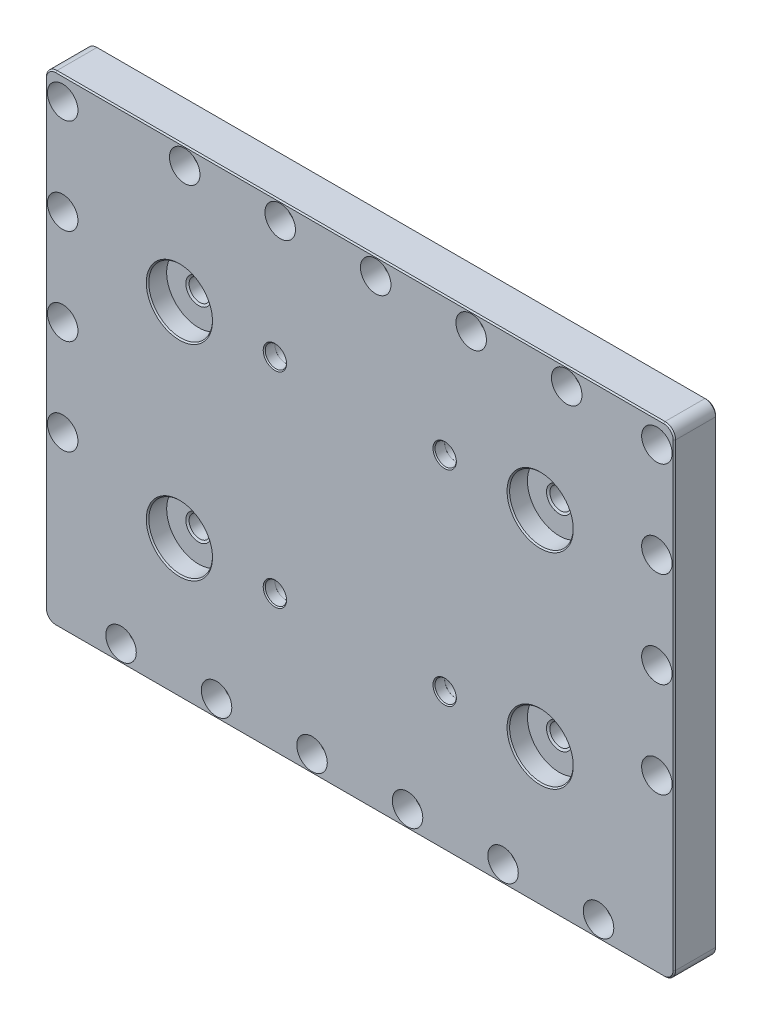
SolidWorks part; units mm, degrees
material "6061-T6 Al"
ref_plane "Front" through (0, 0, 0) normal (0, 0, 1) x (1, 0, 0)
ref_plane "Top" through (0, 0, 0) normal (0, 1, 0) x (1, 0, 0)
ref_plane "Right" through (0, 0, 0) normal (1, 0, 0) x (0, 0, -1)
sketch "Sketch1" plane through (0, 0, 0) normal (0, 0, 1) x (1, 0, 0)
  line L1 (-188.2775, 0) -> (188.2775, 0)
  line L2 (-188.2775, 0) -> (-188.2775, 287.655)
  line L3 (-188.2775, 287.655) -> (188.2775, 287.655)
  line L4 (188.2775, 0) -> (188.2775, 287.655)
  dimension "D1" = 376.555
  dimension "D2" = 287.655
extrude "Extrude1" add sketch "Sketch1" along normal blind 25.4
hole_wizard "CBORE for 3/8 Socket Head Cap Screw3" positions "Sketch8" profile "Sketch7" counterbore size "3/8" standard "Ansi Inch" end condition through all
sketch "Sketch8" plane through (0, 0, 25.4) normal (0, 0, 1) x (1, 0, 0)
  line L0 (-142.875, 10.4775) -> (-85.725, 10.4775) construction
  line L1 (-85.725, 10.4775) -> (-28.575, 10.4775) construction
  line L2 (-28.575, 10.4775) -> (28.575, 10.4775) construction
  line L3 (28.575, 10.4775) -> (85.725, 10.4775) construction
  line L7 (85.725, 10.4775) -> (142.875, 10.4775) construction
  line L14 (0, 10.4775) -> (0, 277.1775) construction
  line L17 (0, 143.8275) -> (188.2775, 143.8275) construction
  line L18 (188.2775, 0) -> (188.2775, 287.655) construction
  line L19 (-188.2775, 287.655) -> (-188.2775, 0) construction
  line L20 (-104.775, 277.1775) -> (-47.625, 277.1775) construction
  line L23 (-47.625, 277.1775) -> (9.525, 277.1775) construction
  line L24 (9.525, 277.1775) -> (66.675, 277.1775) construction
  line L25 (66.675, 277.1775) -> (123.825, 277.1775) construction
  point P0 (-142.875, 10.4775)
  point P1 (-85.725, 10.4775)
  point P3 (-28.575, 10.4775)
  point P5 (28.575, 10.4775)
  point P7 (85.725, 10.4775)
  point P37 (-104.775, 277.1775)
  point P39 (-47.625, 277.1775)
  point P41 (9.525, 277.1775)
  point P43 (66.675, 277.1775)
  point P45 (123.825, 277.1775)
  point P49 (142.875, 10.4775)
  point P78 (0, 10.4775)
  dimension "D1" = 266.7
  dimension "D2" = 57.15
  dimension "D3" = 83.5025
sketch "Sketch7" plane through (-142.875, 10.4775, 25.4) normal (1, 0, 0) x (0, -1, 0)
  line L0 (0, 0) -> (0, 25.4)
  line L1 (5.5626, 24.6126) -> (6.35, 25.4)
  line L2 (5.5626, 24.6126) -> (5.5626, 12.7)
  line L3 (5.5626, 12.7) -> (9.1313, 12.7)
  line L4 (9.1313, 12.7) -> (9.1313, 0)
  line L5 (9.1313, 0) -> (0, 0)
  line L11 (0, -6.35) -> (0, 107.95) construction
  line L12 (6.35, 25.4) -> (0, 25.4)
  line L13 (-5.5626, 24.6126) -> (-6.35, 25.4) construction
  dimension "Thru Hole Dia." = 11.1252
  dimension "Thru Hole Depth" = 25.4
  dimension "C'Bore Dia." = 18.2626
  dimension "C'Bore Depth" = 12.7
  dimension "Far C'Sink Dia." = 12.7
  dimension "Far C'Sink Angle" = 90
hole_wizard "CBORE for 3/8 Socket Head Cap Screw4" positions "Sketch19" profile "Sketch18" counterbore size "3/8" standard "Ansi Inch" end condition through all
sketch "Sketch19" plane through (0, 0, 25.4) normal (0, 0, 1) x (1, 0, 0)
  line L0 (-177.8, 102.5525) -> (177.8, 102.5525) construction
  line L1 (177.8, 102.5525) -> (177.8, 159.7025) construction
  line L2 (177.8, 159.7025) -> (177.8, 216.8525) construction
  line L3 (177.8, 216.8525) -> (177.8, 274.0025) construction
  circle A0 centre (123.825, 277.1775) radius 5.5626 construction
  point P0 (-177.8, 274.0025)
  point P1 (-177.8, 216.8525)
  point P3 (-177.8, 159.7025)
  point P5 (-177.8, 102.5525)
  point P7 (177.8, 274.0025)
  point P9 (177.8, 216.8525)
  point P11 (177.8, 159.7025)
  point P13 (177.8, 102.5525)
  point P29 (0, 102.5525)
  dimension "D1" = 355.6
  dimension "D2" = 57.15
  dimension "D3" = 3.175
sketch "Sketch18" plane through (-177.8, 274.0025, 25.4) normal (1, 0, 0) x (0, -1, 0)
  line L0 (0, 0) -> (0, 25.4)
  line L1 (5.5626, 24.6126) -> (6.35, 25.4)
  line L2 (5.5626, 24.6126) -> (5.5626, 14.224)
  line L3 (5.5626, 14.224) -> (9.1313, 14.224)
  line L4 (9.1313, 14.224) -> (9.1313, 0)
  line L5 (9.1313, 0) -> (0, 0)
  line L11 (0, -6.35) -> (0, 107.95) construction
  line L12 (6.35, 25.4) -> (0, 25.4)
  line L13 (-5.5626, 24.6126) -> (-6.35, 25.4) construction
  dimension "Thru Hole Dia." = 11.1252
  dimension "Thru Hole Depth" = 25.4
  dimension "C'Bore Dia." = 18.2626
  dimension "C'Bore Depth" = 14.224
  dimension "Far C'Sink Dia." = 12.7
  dimension "Far C'Sink Angle" = 90
fillet "Fillet3" radius 6.35 4 edges at (188.2775, 287.655, 12.7) (188.2775, 0, 12.7) (-188.2775, 0, 12.7) (-188.2775, 287.655, 12.7)
chamfer "Chamfer3" distance 0.762 angle 45 16 edges at (0, 0, 0) (186.4176, 1.8599, 0) (-186.4176, 1.8599, 0) (188.2775, 143.8275, 0) (-188.2775, 143.8275, 0) (186.4176, 285.7951, 0) (-186.4176, 285.7951, 0) (0, 287.655, 0) (0, 0, 25.4) (186.4176, 1.8599, 25.4) (-186.4176, 1.8599, 25.4) (188.2775, 143.8275, 25.4) (-188.2775, 143.8275, 25.4) (186.4176, 285.7951, 25.4) (-186.4176, 285.7951, 25.4) (0, 287.655, 25.4)
hole_wizard "CBORE for 1/2 Socket Head Cap Screw1" positions "Sketch24" profile "Sketch23" counterbore size "1/2" standard "Ansi Inch" end condition through all
sketch "Sketch24" plane through (0, 0, 25.4) normal (0, 0, 1) x (1, 0, 0)
  line L0 (-50.8, 82.55) -> (50.8, 82.55) construction
  line L8 (-50.8, 205.105) -> (50.8, 205.105) construction
  line L9 (-181.9275, 287.655) -> (181.9275, 287.655) construction
  line L10 (0, 0) -> (0, 82.55) construction
  point P0 (-50.8, 205.105)
  point P1 (50.8, 205.105)
  point P3 (-50.8, 82.55)
  point P5 (50.8, 82.55)
  dimension "D1" = 101.6
  dimension "D2" = 205.105
  dimension "D3" = 82.55
sketch "Sketch23" plane through (-50.8, 205.105, 25.4) normal (1, 0, 0) x (0, -1, 0)
  line L0 (0, 0) -> (0, 25.4)
  line L1 (6.35, 24.765) -> (6.985, 25.4)
  line L2 (6.3754, 6.35) -> (6.35, 6.35)
  line L3 (6.35, 6.35) -> (6.35, 24.765)
  line L5 (6.3754, 6.35) -> (6.3754, 0.6096)
  line L6 (6.3754, 0.6096) -> (6.985, 0)
  line L7 (6.985, 0) -> (0, 0)
  line L8 (-6.3754, 0.6096) -> (-6.985, 0) construction
  line L11 (0, -6.35) -> (0, 107.95) construction
  line L12 (6.985, 25.4) -> (0, 25.4)
  line L13 (-6.35, 24.765) -> (-6.985, 25.4) construction
  dimension "Thru Hole Dia." = 12.7
  dimension "Thru Hole Depth" = 25.4
  dimension "C'Bore Dia." = 12.7508
  dimension "C'Bore Depth" = 6.35
  dimension "Near C'Sink Dia." = 13.97
  dimension "Near C'Sink Angle" = 90
  dimension "Far C'Sink Dia." = 13.97
  dimension "Far C'Sink Angle" = 90
sketch "Sketch29" plane through (0, 0, 25.4) normal (0, 0, 1) x (1, 0, 0)
  line L0 (-107.95, 205.105) -> (-50.8, 205.105) construction
  line L1 (-50.8, 82.55) -> (-50.8, 205.105) construction
  line L2 (-50.8, 143.8275) -> (0, 143.8275) construction
  line L3 (0, 143.8275) -> (0, 0) construction
  circle A0 centre (-107.95, 205.105) radius 19.05
  circle A1 centre (-107.95, 82.55) radius 19.05
  circle A2 centre (107.95, 82.55) radius 19.05
  circle A3 centre (107.95, 205.105) radius 19.05
  dimension "D1" = 38.1
  dimension "D2" = 215.9
extrude "Extrude8" cut sketch "Sketch29" against normal blind 11.43
hole_wizard "1/2-13 Tapped Hole1" positions "Sketch31" profile "Sketch30" tap size "1/2-13" standard "Ansi Inch" end condition through all
sketch "Sketch31" plane through (0, 0, 13.97) normal (0, 0, 1) x (1, 0, 0)
  point P0 (-107.95, 205.105)
  point P1 (107.95, 205.105)
  point P4 (107.95, 82.55)
  point P7 (-107.95, 82.55)
sketch "Sketch30" plane through (-107.95, 205.105, 13.97) normal (1, 0, 0) x (0, -1, 0)
  line L0 (0, 0) -> (0, 13.97)
  line L1 (0, 13.97) -> (8.89, 13.97)
  line L2 (6.35, 12.5035) -> (6.35, 0.7332)
  line L3 (6.35, 0.7332) -> (7.62, 0)
  line L5 (7.62, 0) -> (0, 0)
  line L6 (-6.35, 0.7332) -> (-7.62, 0) construction
  line L7 (8.89, 13.97) -> (6.35, 12.5035)
  line L8 (-8.89, 13.97) -> (-6.35, 12.5035) construction
  line L11 (0, -6.35) -> (0, 107.95) construction
  dimension "Thread Major Dia." = 12.7
  dimension "Thru Tap Drill Depth" = 13.97
  dimension "Near C'Sink Dia." = 15.24
  dimension "Near C'Sink Angle" = 120
  dimension "Far C'Sink Dia." = 17.78
  dimension "Far C'Sink Angle" = 120
chamfer "Chamfer5" distance 0.762 angle 45 4 edges at (-127, 82.55, 25.4) (127, 82.55, 25.4) (88.9, 205.105, 25.4) (-88.9, 205.105, 25.4)
